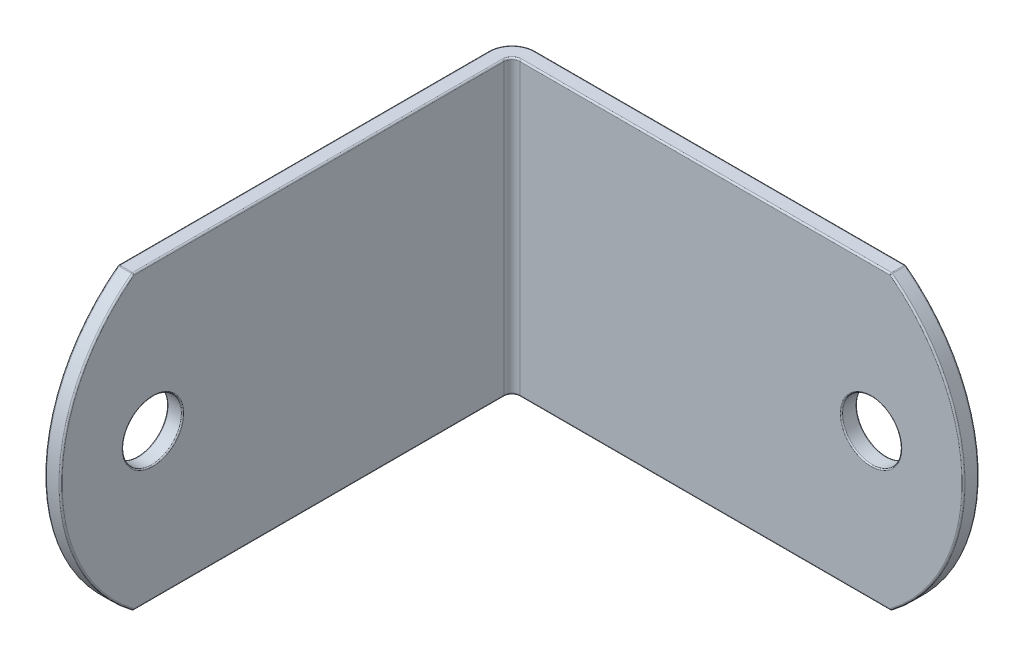
SolidWorks part; units mm, degrees
ref_plane "Front Plane" through (0, 0, 0) normal (0, 0, 1) x (1, 0, 0)
ref_plane "Top Plane" through (0, 0, 0) normal (0, 1, 0) x (1, 0, 0)
ref_plane "Right Plane" through (0, 0, 0) normal (1, 0, 0) x (0, 0, -1)
sketch "Sketch1" plane through (0, 0, 0) normal (0, 1, 0) x (1, 0, 0)
  line L0 (-19.05, -19.05) -> (-19.05, 19.05)
  line L1 (-19.05, 19.05) -> (19.05, 19.05)
  line L2 (-19.05, -19.05) -> (-17.78, -19.05)
  line L3 (-17.78, -19.05) -> (-17.78, 17.78)
  line L4 (-17.78, 17.78) -> (19.05, 17.78)
  line L5 (19.05, 17.78) -> (19.05, 19.05)
  line L6 (11.5094, 19.05) -> (11.5094, 17.78) construction
  line L7 (-19.05, -11.5094) -> (-17.78, -11.5094) construction
  line L8 (13.9224, 19.05) -> (13.9224, 17.78)
  line L9 (-19.05, -9.0964) -> (-17.78, -9.0964)
  line L10 (-19.05, -13.9224) -> (-17.78, -13.9224)
  line L11 (9.0964, 19.05) -> (9.0964, 17.78)
  arc A0 (-19.05, 17.145) -> (-17.145, 19.05) centre (-17.145, 17.145) cw
  arc A1 (-17.78, 17.145) -> (-17.145, 17.78) centre (-17.145, 17.145) cw
  point P2 (-19.05, 0)
  point P5 (0, 19.05)
  point P27 (-17.78, -13.9224)
  point P29 (9.0964, 17.78)
  dimension "D1" = 0.635
  dimension "Length (B)" = 38.1
  dimension "Length (A)" = 38.1
  dimension "Thickness" = 1.27
  dimension "Mounting Hole Location 2" = 7.5406
  dimension "Mounting Hole Location 1" = 7.5406
  dimension "Mounting Hole Diameter 2" = 4.826
  dimension "Mounting Hole Diameter 1" = 4.826
sketch "Sketch2" plane through (0, 0, 0) normal (1, 0, 0) x (0, 0, -1)
  line L0 (0, 11.9062) -> (0, -11.9062)
  arc A0 (-13.0969, 11.9062) -> (-13.0969, -11.9062) centre (-4.1672, 0) ccw
  point P2 (0, 0)
  point P10 (-19.05, 0)
  dimension "Length (C)" = 23.8125
  dimension "D1" = 5.9531
sketch "Sketch4" plane through (0, 0, 0) normal (0, 1, 0) x (1, 0, 0)
  line L0 (-19.05, -19.05) -> (-17.78, -19.05) construction
  line L1 (-17.78, -19.05) -> (-17.78, 17.78) construction
  line L2 (-17.78, 17.78) -> (19.05, 17.78) construction
  line L3 (19.05, 17.78) -> (19.05, 19.05) construction
  line L4 (-19.05, 19.05) -> (19.05, 19.05) construction
  line L5 (-19.05, -19.05) -> (-19.05, 19.05) construction
  line L6 (-19.05, -19.05) -> (-17.78, -19.05)
  line L7 (-17.78, -19.05) -> (-17.78, 17.145)
  line L8 (-17.145, 17.78) -> (19.05, 17.78)
  line L9 (19.05, 17.78) -> (19.05, 19.05)
  line L10 (-17.145, 19.05) -> (19.05, 19.05)
  line L11 (-19.05, -19.05) -> (-19.05, 17.145)
  arc A0 (-17.145, 17.78) -> (-17.78, 17.145) centre (-17.145, 17.145) ccw construction
  arc A1 (-17.145, 19.05) -> (-19.05, 17.145) centre (-17.145, 17.145) ccw construction
  arc A2 (-17.145, 17.78) -> (-17.78, 17.145) centre (-17.145, 17.145) ccw
  arc A3 (-17.145, 19.05) -> (-19.05, 17.145) centre (-17.145, 17.145) ccw
extrude "Boss-Extrude1" add sketch "Sketch4" against normal up to vertex (11.9062 mm away) from vertex at 11.9062 starting at point (0, 11.9062, 0)
sketch "Sketch5" plane through (0, 0, 0) normal (0, 1, 0) x (1, 0, 0)
  line L1 (-19.05, -11.5094) -> (-17.78, -11.5094)
  line L2 (-19.05, -11.5094) -> (-19.05, -9.0964)
  line L3 (-19.05, -9.0964) -> (-17.78, -9.0964)
  line L4 (-17.78, -11.5094) -> (-17.78, -9.0964)
revolve "Cut-Revolve1" cut sketch "Sketch5" angle 360 about L1
sketch "Sketch6" plane through (0, 0, 0) normal (0, 1, 0) x (1, 0, 0)
  line L1 (11.5094, 19.05) -> (13.9224, 19.05)
  line L2 (11.5094, 19.05) -> (11.5094, 17.78)
  line L3 (11.5094, 17.78) -> (13.9224, 17.78)
  line L4 (13.9224, 19.05) -> (13.9224, 17.78)
revolve "Cut-Revolve2" cut sketch "Sketch6" angle 360 about L2
sketch "Sketch7" plane through (-17.78, 0, 0) normal (1, 0, 0) x (0, 0, -1)
  line L0 (-13.0969, 11.9063) -> (-19.05, 11.9062)
  line L1 (-19.05, 11.9062) -> (-19.05, 0)
  line L2 (-19.05, 0) -> (-19.05, -11.9062)
  line L3 (-19.05, -11.9062) -> (-13.0969, -11.9063)
  arc A0 (-13.0969, 11.9063) -> (-13.0969, -11.9063) centre (-4.1672, 0) ccw construction
  arc A1 (-13.0969, 11.9063) -> (-13.0969, -11.9063) centre (-4.1672, 0) ccw
  line M2 (17.145, 11.9062) -> (-19.05, 11.9062)
  line M3 (-19.05, 11.9062) -> (-19.05, -11.9062)
  line M4 (-19.05, -11.9062) -> (17.145, -11.9062)
extrude "Cut-Extrude1" cut sketch "Sketch7" against normal through all contours A1 M2 M3 | A1 M3 M4
sketch "Sketch8" plane through (0, 0, -17.78) normal (0, 0, 1) x (1, 0, 0)
  line L0 (-17.145, 11.9062) -> (19.05, 11.9062) construction
  line L1 (-17.145, -11.9062) -> (19.05, -11.9062) construction
  line L3 (13.0969, 11.9062) -> (19.05, 11.9062)
  line L4 (19.05, 11.9062) -> (19.05, 0)
  line L5 (19.05, 0) -> (19.05, -11.9062)
  line L6 (19.05, -11.9062) -> (13.0969, -11.9062)
  arc A0 (13.0969, 11.9062) -> (13.0969, -11.9062) centre (4.1672, 0) cw
  line M2 (19.05, 11.9062) -> (-17.145, 11.9062)
  line M4 (-17.145, -11.9062) -> (19.05, -11.9062)
  line M5 (19.05, -11.9062) -> (19.05, 11.9062)
  dimension "D1" = 5.9531
extrude "Cut-Extrude2" cut sketch "Sketch8" against normal through all contours A0 M2 M5 | A0 M5 M4
fillet "Fillet1" radius 0.127 20 edges at (-19.05, -11.9062, -2.0241) (-18.492, -11.9062, -18.492) (-19.05, 11.9062, -2.0241) (-18.492, 11.9062, -18.492) (-2.0241, -11.9062, -17.78) (-17.594, -11.9062, -17.594) (-2.0241, 11.9062, -17.78) (-17.594, 11.9062, -17.594) (-18.415, -11.9062, 13.0969) (13.0969, -11.9062, -18.415) (13.0969, 11.9062, -18.415) (-18.415, 11.9062, 13.0969) (-2.0241, -11.9062, -19.05) (-2.0241, 11.9062, -19.05) (19.05, 0, -19.05) (19.05, 0, -17.78) (-17.78, -11.9062, -2.0241) (-17.78, 11.9062, -2.0241) (-19.05, 0, 19.05) (-17.78, 0, 19.05)
fillet "Fillet2" radius 0.0965 4 edges at (9.0964, 0, -19.05) (-19.05, 0, 13.9224) (9.0964, 0, -17.78) (-17.78, 0, 13.9224)
equation "\"D1@Sketch1\"=\"Thickness@Sketch1\"*0.5"
equation "\"D1@Sketch2\"=\"Length (C)@Sketch2\"*0.25"
equation "\"D1@Sketch8\"=\"D1@Sketch2\""
equation "\"D1@Fillet1\"=0.1*\"Thickness@Sketch1\""
equation "\"D1@Fillet2\"=\"Mounting Hole Diameter 2@Sketch1\"*.02"
